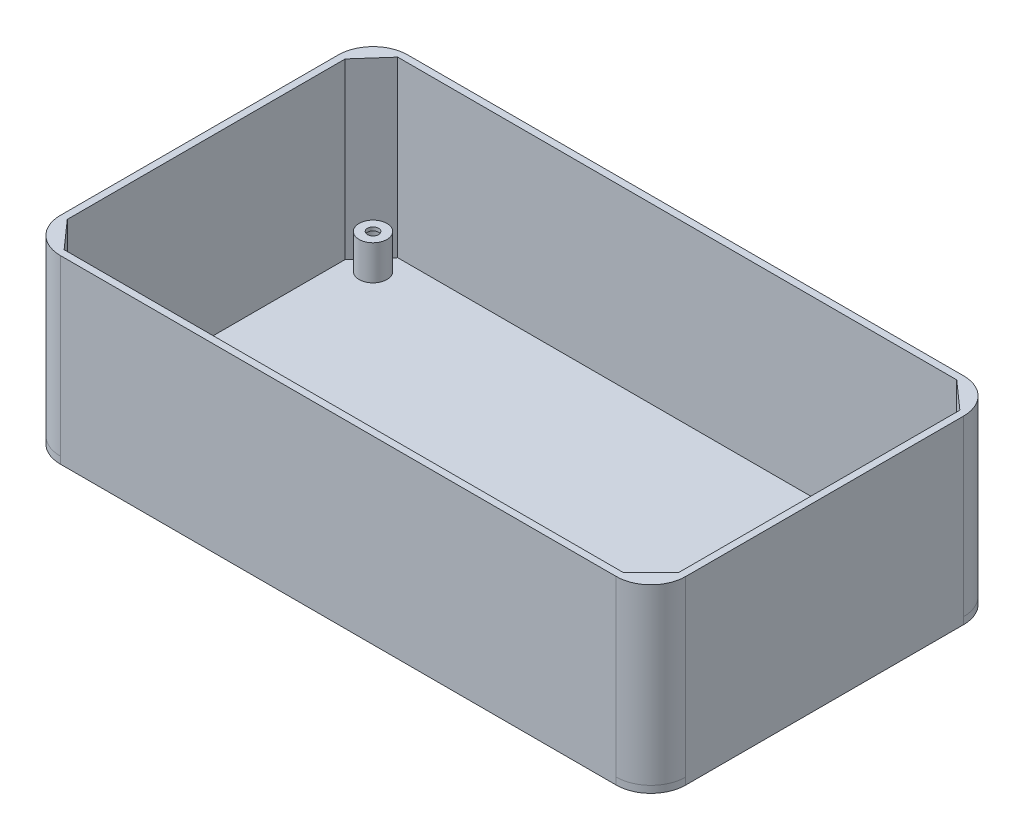
SolidWorks part; units mm, degrees
ref_plane "Спереди" through (0, 0, 0) normal (0, 0, 1) x (1, 0, 0)
ref_plane "Сверху" through (0, 0, 0) normal (0, 1, 0) x (1, 0, 0)
ref_plane "Справа" through (0, 0, 0) normal (1, 0, 0) x (0, 0, -1)
sketch "Эскиз1" plane through (0, 0, 0) normal (0, 1, 0) x (1, 0, 0)
  line L1 (-70.0914, 46.5631) -> (109.9086, 46.5631)
  line L2 (-70.0914, 46.5631) -> (-70.0914, -53.4369)
  line L3 (-70.0914, -53.4369) -> (109.9086, -53.4369)
  line L4 (109.9086, 46.5631) -> (109.9086, -53.4369)
  dimension "D1" = 180
  dimension "D2" = 100
extrude "Бобышка-Вытянуть1" add sketch "Эскиз1" along normal blind 2
fillet "Скругление2" radius 10 4 edges at (109.9086, 1, -46.5631) (109.9086, 1, 53.4369) (-70.0914, 1, 53.4369) (-70.0914, 1, -46.5631)
sketch "Эскиз2" plane through (0, 2, 0) normal (0, 1, 0) x (1, 0, 0)
  line L0 (99.9086, 46.5631) -> (-60.0914, 46.5631)
  line L1 (-60.0914, 46.5631) -> (-70.0914, 46.5631)
  line L2 (-70.0914, 46.5631) -> (-70.0914, 36.5631)
  line L3 (-70.0914, 36.5631) -> (-70.0914, -43.4369)
  line L4 (-70.0914, -43.4369) -> (-70.0914, -53.4369)
  line L5 (-70.0914, -53.4369) -> (-60.0914, -53.4369)
  line L6 (-60.0914, -53.4369) -> (99.9086, -53.4369) construction
  line L7 (-60.0914, -53.4369) -> (99.9086, -53.4369)
  line L8 (99.9086, -53.4369) -> (109.9086, -53.4369)
  line L9 (109.9086, -53.4369) -> (109.9086, -43.4369)
  line L10 (109.9086, -43.4369) -> (109.9086, 36.5631)
  line L11 (109.9086, 36.5631) -> (109.9086, 46.5631)
  line L12 (109.9086, 46.5631) -> (99.9086, 46.5631)
  line L13 (-68.0914, -43.4369) -> (-68.0914, 36.5631)
  line L19 (-60.9874, 44.5631) -> (99.9086, 44.5631)
  line L21 (107.9086, 37.459) -> (107.9086, -43.4369)
  line L23 (99.9086, -51.4369) -> (-60.9874, -51.4369)
  line L25 (-68.0914, -43.4369) -> (-60.9874, -51.4369)
  line L26 (99.9086, -51.4369) -> (107.9086, -43.4369)
  line L27 (99.9086, 44.5631) -> (107.9086, 37.459)
  line L28 (-60.9874, 44.5631) -> (-68.0914, 36.5631)
  arc A0 (-70.0914, -43.4369) -> (-60.0914, -53.4369) centre (-60.0914, -43.4369) ccw construction
  point P34 (99.9086, -51.4369)
  point P35 (107.9086, -43.4369)
  point P36 (99.9086, -51.4369)
  point P37 (107.9086, -43.4369)
  point P38 (107.9086, 36.5631)
  point P39 (99.9086, 44.5631)
  dimension "D1" = 2
  dimension "D2" = 2
  dimension "D3" = 2
  dimension "D4" = 2
sketch "Эскиз3" plane through (0, 2, 0) normal (0, 1, 0) x (1, 0, 0)
  line L0 (99.9086, 46.5631) -> (-60.0914, 46.5631) construction
  line L1 (-70.0914, 36.5631) -> (-70.0914, -43.4369) construction
  line L2 (109.9086, -43.4369) -> (109.9086, 36.5631) construction
  line L3 (-60.0914, -53.4369) -> (99.9086, -53.4369) construction
  circle A0 centre (-61.0914, 37.5631) radius 4
  circle A1 centre (100.9086, 37.5631) radius 4
  circle A2 centre (100.9086, -44.4369) radius 4
  circle A3 centre (-61.0914, -44.4369) radius 4
  dimension "D1" = 9
  dimension "D2" = 9
  dimension "D3" = 9
  dimension "D4" = 9
  dimension "D5" = 9
  dimension "D6" = 9
  dimension "D7" = 9
  dimension "D8" = 9
extrude "Бобышка-Вытянуть2" add sketch "Эскиз3" along normal blind 10
sketch "Эскиз4" plane through (0, 0, 0) normal (0, -1, 0) x (1, 0, 0)
  line L0 (-70.0914, -36.5631) -> (-70.0914, 43.4369) construction
  line L1 (99.9086, -46.5631) -> (-60.0914, -46.5631) construction
  line L2 (-60.0914, 53.4369) -> (99.9086, 53.4369) construction
  line L3 (109.9086, 43.4369) -> (109.9086, -36.5631) construction
  circle A0 centre (-61.0914, -37.5631) radius 3
  circle A1 centre (-61.0914, 44.4369) radius 3
  circle A2 centre (100.9086, 44.4369) radius 3
  circle A3 centre (100.9086, -37.5631) radius 3
  dimension "D1" = 9
  dimension "D2" = 9
  dimension "D3" = 9
  dimension "D4" = 9
  dimension "D5" = 9
  dimension "D6" = 9
  dimension "D7" = 9
  dimension "D8" = 9
extrude "Вырез-Вытянуть1" cut sketch "Эскиз4" against normal blind 11
sketch "Эскиз5" plane through (0, 12, 0) normal (0, 1, 0) x (1, 0, 0)
  circle A0 centre (100.9086, 37.5631) radius 1.6
  circle A1 centre (100.9086, 37.5631) radius 4 construction
  circle A2 centre (100.9086, -44.4369) radius 1.6
  circle A3 centre (-61.0914, 37.5631) radius 1.6
  circle A4 centre (-61.0914, -44.4369) radius 1.6
  circle A5 centre (-61.0914, -44.4369) radius 4 construction
  circle A6 centre (-61.0914, 37.5631) radius 4 construction
  circle A7 centre (100.9086, -44.4369) radius 4 construction
  dimension "D1" = 0
  dimension "D2" = 0
  dimension "D3" = 0
  dimension "D4" = 0
  dimension "D5" = 0
extrude "Вырез-Вытянуть2" cut sketch "Эскиз5" against normal through all
sketch "Эскиз6" plane through (0, 2, 0) normal (0, 1, 0) x (1, 0, 0)
  line L1 (-70.0914, -53.4369) -> (109.9086, -53.4369)
  line L2 (-70.0914, -53.4369) -> (-70.0914, 46.5631)
  line L3 (-70.0914, 46.5631) -> (109.9086, 46.5631)
  line L4 (109.9086, -53.4369) -> (109.9086, 46.5631)
  line L5 (-68.0914, -51.4369) -> (107.9086, -51.4369)
  line L6 (-68.0914, -51.4369) -> (-68.0914, 44.5631)
  line L7 (-68.0914, 44.5631) -> (107.9086, 44.5631)
  line L8 (107.9086, -51.4369) -> (107.9086, 44.5631)
extrude "Бобышка-Вытянуть4" add sketch "Эскиз6" along normal blind 50
extrude "Бобышка-Вытянуть5" add sketch "Эскиз2" along normal blind 50
fillet "Скругление4" radius 10 4 edges at (-70.0914, 27, 53.4369) (-70.0914, 27, -46.5631) (109.9086, 27, -46.5631) (109.9086, 27, 53.4369)
